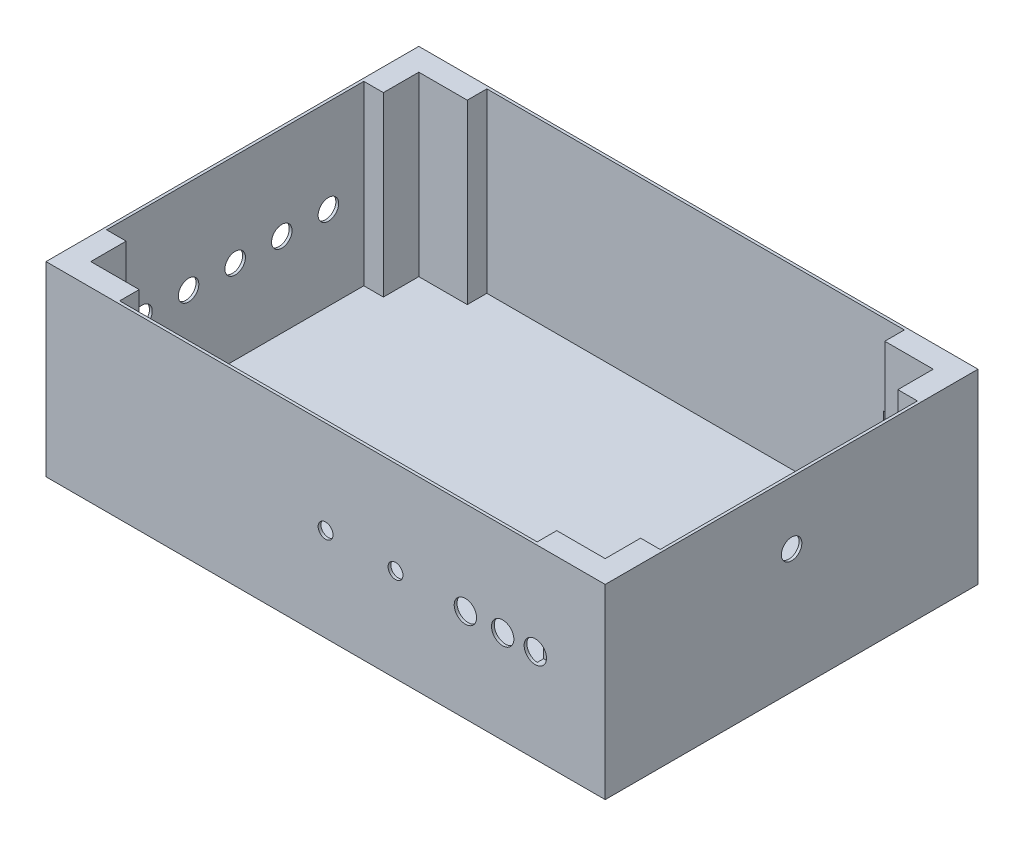
SolidWorks part; units mm, degrees
ref_plane "Płaszczyzna przednia" through (0, 0, 0) normal (0, 0, 1) x (1, 0, 0)
ref_plane "Płaszczyzna górna" through (0, 0, 0) normal (0, 1, 0) x (1, 0, 0)
ref_plane "Płaszczyzna prawa" through (0, 0, 0) normal (1, 0, 0) x (0, 0, -1)
sketch "Sketch1" plane through (0, 0, 0) normal (0, 1, 0) x (1, 0, 0)
  line L1 (-300, -200) -> (300, -200)
  line L2 (-300, -200) -> (-300, 200)
  line L3 (-300, 200) -> (300, 200)
  line L4 (300, -200) -> (300, 200)
  line L5 (-300, -200) -> (300, 200) construction
  line L6 (-300, 200) -> (300, -200) construction
  point P0 (0, 0)
  dimension "D1" = 600
  dimension "D2" = 400
extrude "Boss-Extrude1" add sketch "Sketch1" along normal blind 200
sketch "Sketch2" plane through (0, 200, 0) normal (0, 1, 0) x (1, 0, 0)
  line L0 (300, 200) -> (-300, 200) construction
  line L1 (-224, -197) -> (224, -197)
  line L2 (-297, -138) -> (-297, 138)
  line L3 (-224, 197) -> (224, 197)
  line L4 (297, -138) -> (297, 138)
  line L5 (-297, -197) -> (297, 197) construction
  line L6 (-297, 197) -> (297, -197) construction
  line L9 (-276, 176) -> (-224, 176)
  line L10 (-224, 197) -> (-224, 176)
  line L11 (-300, 200) -> (-300, -200) construction
  line L12 (300, -200) -> (300, 200) construction
  line L15 (-297, 138) -> (-276, 138)
  line L16 (-276, 176) -> (-276, 138)
  line L19 (297, 138) -> (276, 138)
  line L23 (276, 176) -> (224, 176)
  line L24 (224, 197) -> (224, 176)
  line L25 (-300, -200) -> (300, -200) construction
  line L28 (297, -138) -> (276, -138)
  line L29 (276, -176) -> (276, -138)
  line L32 (276, -176) -> (224, -176)
  line L33 (224, -197) -> (224, -176)
  line L34 (276, 176) -> (276, 138)
  line L37 (-276, -176) -> (-224, -176)
  line L38 (-224, -197) -> (-224, -176)
  line L41 (-297, -138) -> (-276, -138)
  line L42 (-276, -176) -> (-276, -138)
  point P0 (0, 0)
  dimension "D1" = 594
  dimension "D2" = 394
  dimension "D3" = 24
  dimension "D4" = 76
  dimension "D5" = 62
  dimension "D6" = 24
  dimension "D7" = 24
  dimension "D8" = 76
  dimension "D10" = 62
  dimension "D11" = 62
  dimension "D12" = 76
  dimension "D13" = 24
  dimension "D14" = 24
extrude "Cut-Extrude1" cut sketch "Sketch2" against normal blind 190
sketch "Sketch3" plane through (-300, 0, 0) normal (-1, 0, 0) x (0, 0, 1)
  line L0 (-200, 100) -> (200, 100) construction
  line L1 (-200, 200) -> (-200, 0) construction
  line L2 (200, 200) -> (200, 0) construction
  line L3 (-200, 100) -> (0, 100) construction
  line L4 (0, 100) -> (-50, 100) construction
  line L5 (-50, 100) -> (-100, 100) construction
  line L6 (0, 100) -> (50, 100) construction
  line L7 (50, 100) -> (100, 100) construction
  circle A0 centre (-100, 100) radius 11
  circle A1 centre (-50, 100) radius 11
  circle A2 centre (50, 100) radius 11
  circle A3 centre (100, 100) radius 11
  circle A4 centre (0, 100) radius 11
  dimension "D5" = 22
  dimension "D1" = 50
  dimension "D2" = 50
  dimension "D3" = 50
  dimension "D4" = 50
extrude "Cut-Extrude2" cut sketch "Sketch3" against normal blind 10
sketch "Sketch4" plane through (0, 0, 200) normal (0, 0, 1) x (1, 0, 0)
  line L0 (300, 100) -> (-300, 100) construction
  line L1 (300, 200) -> (300, 0) construction
  line L2 (-300, 200) -> (-300, 0) construction
  line L3 (0, 100) -> (75, 100) construction
  line L4 (75, 100) -> (150, 100) construction
  line L5 (150, 100) -> (225, 100) construction
  line L6 (150, 100) -> (190, 100) construction
  circle A0 centre (150, 100) radius 12
  circle A1 centre (75, 100) radius 8
  circle A2 centre (225, 100) radius 12
  circle A3 centre (0, 100) radius 8
  circle A4 centre (190, 100) radius 12
  dimension "D3" = 75
  dimension "D4" = 16
  dimension "D5" = 16
  dimension "D6" = 24
  dimension "D7" = 24
  dimension "D9" = 24
  dimension "D1" = 75
  dimension "D2" = 75
  dimension "D8" = 40
extrude "Cut-Extrude3" cut sketch "Sketch4" against normal blind 10
sketch "Sketch5" plane through (0, 0, -200) normal (0, 0, -1) x (-1, 0, 0)
  line L0 (-300, 100) -> (300, 100) construction
  line L1 (-300, 200) -> (-300, 0) construction
  line L2 (300, 200) -> (300, 0) construction
  line L3 (-300, 100) -> (-225, 100) construction
  line L5 (-248.5, 86.5) -> (-201.5, 86.5)
  line L6 (-248.5, 86.5) -> (-248.5, 113.5)
  line L7 (-248.5, 113.5) -> (-201.5, 113.5)
  line L8 (-201.5, 86.5) -> (-201.5, 113.5)
  line L9 (-248.5, 86.5) -> (-201.5, 113.5) construction
  line L10 (-248.5, 113.5) -> (-201.5, 86.5) construction
  dimension "D1" = 75
  dimension "D2" = 27
  dimension "D3" = 47
extrude "Cut-Extrude4" cut sketch "Sketch5" against normal blind 10
sketch "Sketch6" plane through (300, 0, 0) normal (1, 0, 0) x (0, 0, -1)
  line L0 (-200, 100) -> (200, 100) construction
  line L1 (-200, 200) -> (-200, 0) construction
  line L2 (200, 200) -> (200, 0) construction
  line L3 (0, 0) -> (0, 100) construction
  line L4 (0, 100) -> (0, 200) construction
  line L5 (-200, 200) -> (200, 200) construction
  line L6 (0, 100) -> (0, 133) construction
  circle A0 centre (0, 133) radius 11
  dimension "D2" = 22
  dimension "D1" = 33
extrude "Cut-Extrude5" cut sketch "Sketch6" against normal blind 10
